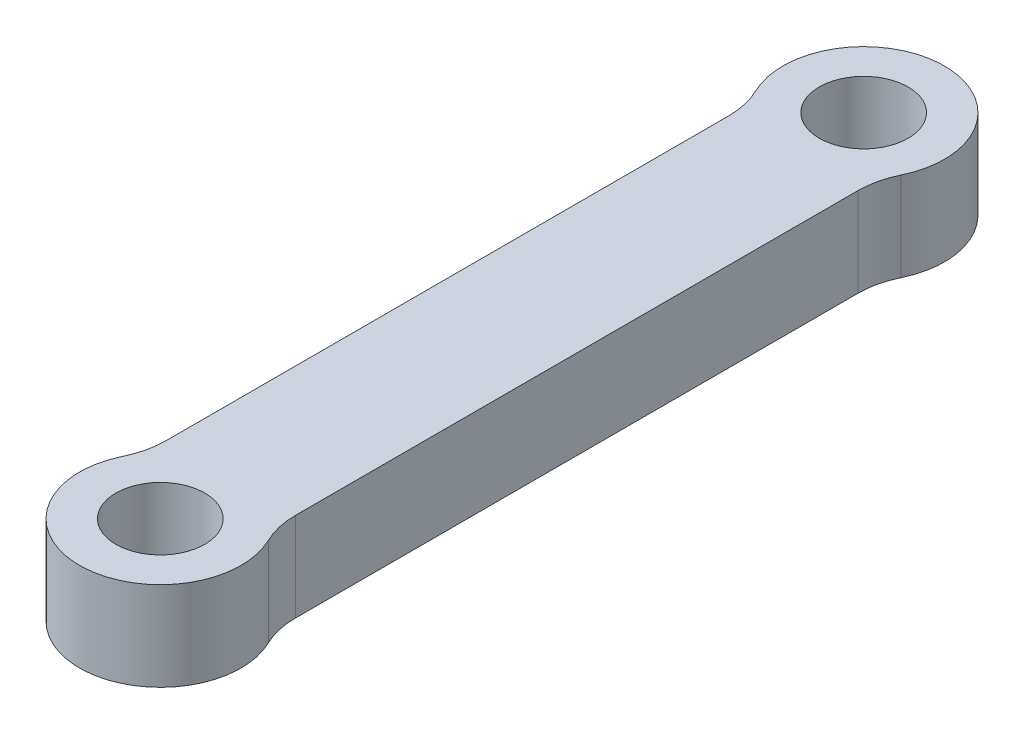
SolidWorks part; units mm, degrees
material "Nylon 101"
ref_plane "Front Plane" through (0, 0, 0) normal (0, 0, 1) x (1, 0, 0)
ref_plane "Top Plane" through (0, 0, 0) normal (0, 1, 0) x (1, 0, 0)
ref_plane "Right Plane" through (0, 0, 0) normal (1, 0, 0) x (0, 0, -1)
sketch "Sketch1" plane through (0, 0, 0) normal (0, 1, 0) x (1, 0, 0)
  line L2 (-4, -21.75) -> (-4, 21.75)
  line L4 (4, -21.75) -> (4, 21.75)
  line L5 (-4, -21.75) -> (4, 21.75) construction
  line L6 (-4, 21.75) -> (4, -21.75) construction
  arc A0 (4, 21.75) -> (-4, 21.75) centre (0, 21.75) ccw
  arc A1 (-4, -21.75) -> (4, -21.75) centre (0, -21.75) ccw
  point P0 (0, 0)
  dimension "D2" = 4
  dimension "D1" = 43.5
extrude "Boss-Extrude1" add sketch "Sketch1" along normal blind 5.5
ref_plane "Plane1" through (0, 5.5, 0) normal (0, 1, 0) x (1, 0, 0)
sketch "Sketch2" plane through (0, 5.5, 0) normal (0, 1, 0) x (1, 0, 0)
  circle A4 centre (0, 21.75) radius 2.75
  circle A5 centre (0, -21.75) radius 2.75
  dimension "D1" = 5.5
extrude "Cut-Extrude2" cut sketch "Sketch2" against normal through all
sketch "Sketch3" plane through (0, 5.5, 0) normal (0, 1, 0) x (1, 0, 0)
  line L0 (0, 0) -> (5.7918, 0) construction
  circle A0 centre (0, 21.75) radius 5
  circle A1 centre (0, 21.75) radius 2.75
  circle A2 centre (0, 21.75) radius 2.75 construction
  circle A3 centre (0, -21.75) radius 2.75
  circle A4 centre (0, -21.75) radius 5
  dimension "D1" = 10
extrude "Boss-Extrude2" add sketch "Sketch3" against normal up to surface (5.5 mm away) up to face at (0, 0, -19)
fillet "Fillet1" radius 5 4 edges at (-4, 2.75, 18.75) (4, 2.75, 18.75) (4, 2.75, -18.75) (-4, 2.75, -18.75)
